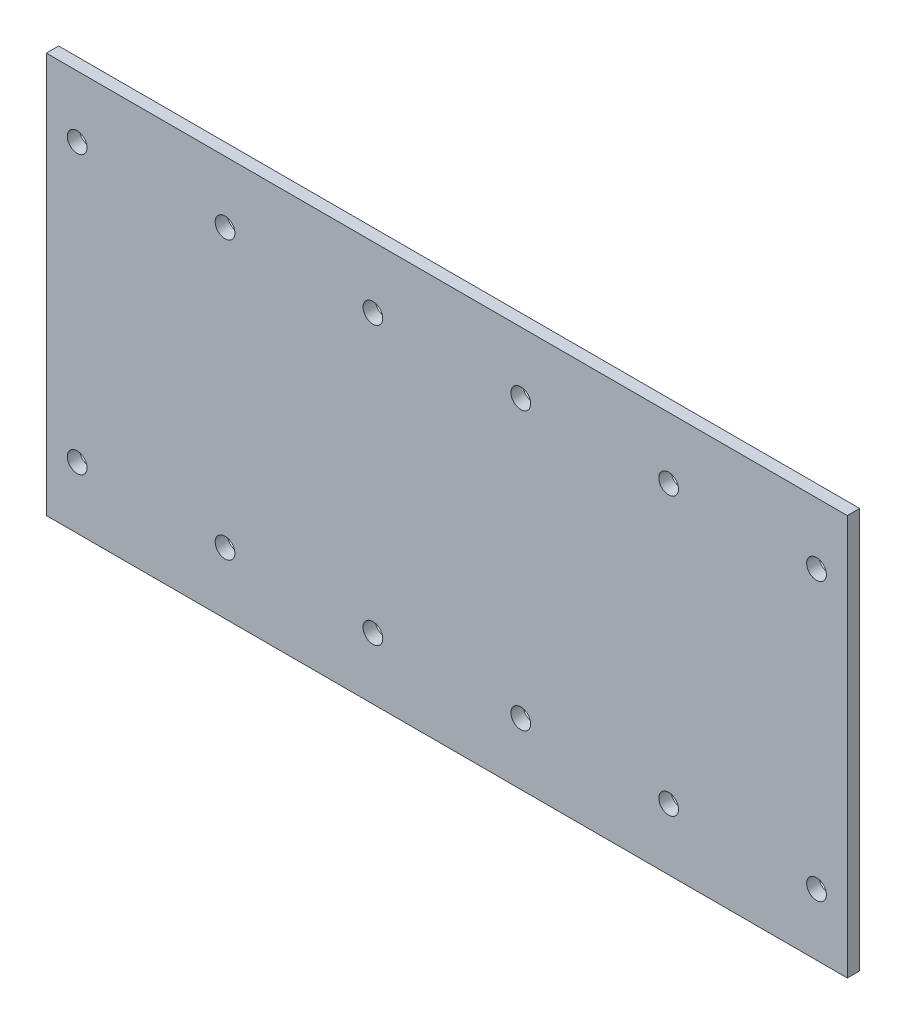
SolidWorks part; units mm, degrees
ref_plane "Plan de face" through (0, 0, 0) normal (0, 0, 1) x (1, 0, 0)
ref_plane "Plan de dessus" through (0, 0, 0) normal (0, 1, 0) x (1, 0, 0)
ref_plane "Plan de droite" through (0, 0, 0) normal (1, 0, 0) x (0, 0, -1)
sketch "Esquisse1" plane through (0, 0, 0) normal (0, 0, 1) x (1, 0, 0)
  line L0 (8.3958, 55) -> (148.4012, 55) construction
  line L1 (0, 0) -> (130, 0)
  line L2 (0, 0) -> (0, 65)
  line L3 (0, 65) -> (130, 65)
  line L4 (130, 0) -> (130, 65)
  line L5 (-5.5431, 10) -> (148.4012, 10) construction
  circle A1 centre (125, 55) radius 1.6
  circle A2 centre (101, 55) radius 1.6
  circle A3 centre (77, 55) radius 1.6
  circle A4 centre (53, 55) radius 1.6
  circle A5 centre (29, 55) radius 1.6
  circle A6 centre (29, 10) radius 1.6
  circle A7 centre (53, 10) radius 1.6
  circle A8 centre (77, 10) radius 1.6
  circle A9 centre (101, 10) radius 1.6
  circle A10 centre (125, 10) radius 1.6
  circle A11 centre (5, 55) radius 1.6
  circle A12 centre (5, 10) radius 1.6
  dimension "D3" = 5
  dimension "D13" = 24
  dimension "D1" = 130
  dimension "D2" = 65
  dimension "D4" = 24
  dimension "D5" = 24
  dimension "D6" = 24
  dimension "D7" = 24
  dimension "D8" = 5
  dimension "D9" = 24
  dimension "D10" = 24
  dimension "D11" = 24
  dimension "D12" = 24
  dimension "D14" = 24
  dimension "D15" = 10
  dimension "D16" = 10
extrude "Boss.-Extru.1" add sketch "Esquisse1" along normal blind 2
